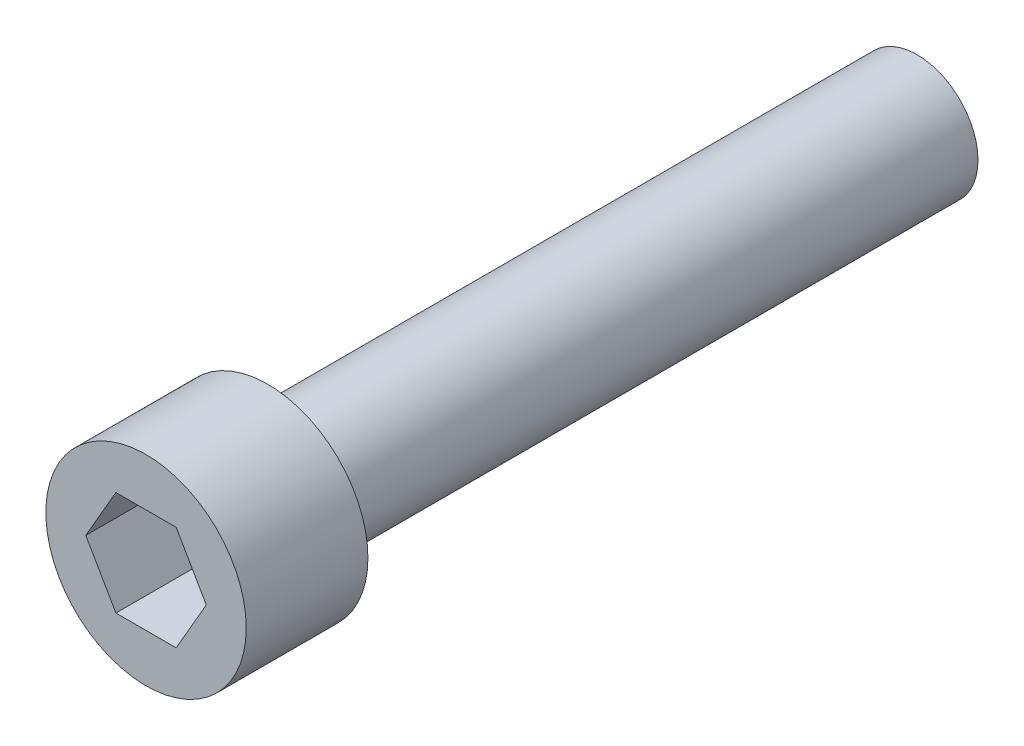
SolidWorks part; units mm, degrees
material "AISI 4340 Steel, normalized"
ref_plane "Front Plane" through (0, 0, 0) normal (0, 0, 1) x (1, 0, 0)
ref_plane "Top Plane" through (0, 0, 0) normal (0, 1, 0) x (1, 0, 0)
ref_plane "Right Plane" through (0, 0, 0) normal (1, 0, 0) x (0, 0, -1)
sketch "Sketch1" plane through (0, 0, 0) normal (0, 1, 0) x (1, 0, 0)
  line L0 (0, 0) -> (0, 26.3906)
  line L1 (0, 26.3906) -> (2.0828, 26.3906)
  line L2 (2.0828, 26.3906) -> (2.0828, 4.1656)
  line L3 (2.0828, 4.1656) -> (3.429, 4.1656)
  line L4 (3.429, 4.1656) -> (3.429, 0)
  line L5 (3.429, 0) -> (0, 0)
  dimension "D1" = 2.0828
  dimension "D2" = 3.429
  dimension "D3" = 4.1656
  dimension "D4" = 22.225
revolve "Revolve1" add sketch "Sketch1" angle 360 about L0
sketch "Sketch2" plane through (0, 0, 0) normal (0, 0, 1) x (1, 0, 0)
  line L1 (2.0622, 0) -> (1.0311, 1.7859)
  line L2 (1.0311, 1.7859) -> (-1.0311, 1.7859)
  line L3 (-1.0311, 1.7859) -> (-2.0622, 0)
  line L4 (-2.0622, 0) -> (-1.0311, -1.7859)
  line L5 (-1.0311, -1.7859) -> (1.0311, -1.7859)
  line L6 (1.0311, -1.7859) -> (2.0622, 0)
  circle A0 centre (0, 0) radius 1.7859 construction
  dimension "D1" = 3.5719
extrude "9-64 allen" cut sketch "Sketch2" against normal blind 3.175
